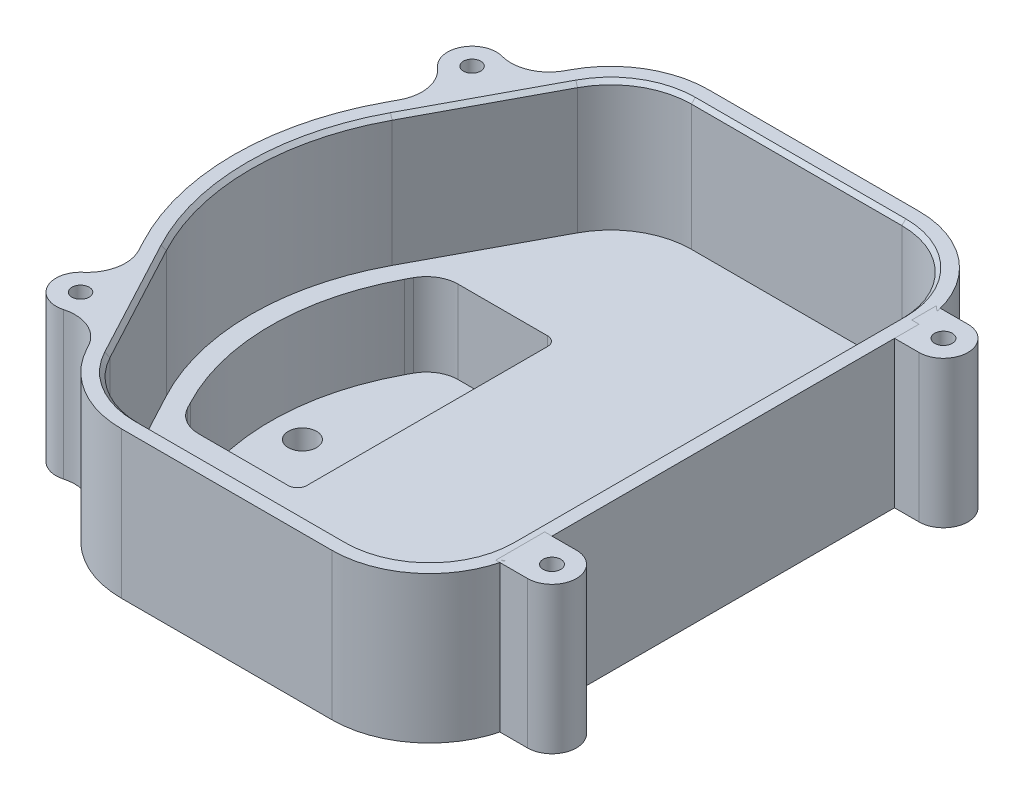
SolidWorks part; units mm, degrees
material "6061-T6 (SS)"
ref_plane "Front Plane" through (0, 0, 0) normal (0, 0, 1) x (1, 0, 0)
ref_plane "Top Plane" through (0, 0, 0) normal (0, 1, 0) x (1, 0, 0)
ref_plane "Right Plane" through (0, 0, 0) normal (1, 0, 0) x (0, 0, -1)
sketch "Sketch1" plane through (0, 0, 0) normal (0, 1, 0) x (1, 0, 0)
  line L0 (-57.15, 0) -> (-57.15, -50000) construction
  line L1 (-25.4, -76.2) -> (-25.4, -101.6) construction
  line L2 (-25.4, -76.2) -> (69.85, -76.2)
  line L3 (-25.4, 76.2) -> (69.85, 76.2)
  line L4 (69.85, -76.2) -> (69.85, 76.2)
  line L5 (-25.4, 76.2) -> (-25.4, 101.6) construction
  line L6 (0, 0) -> (0, -50000) construction
  line L7 (-49.3059, 31.3765) -> (-25.4, 76.2)
  line L8 (-57.15, 0) -> (69.85, 0) construction
  line L9 (-49.3059, -31.3765) -> (-25.4, -76.2)
  arc A0 (-49.3059, -31.3765) -> (-49.3059, 31.3765) centre (9.525, 0) cw
  point P0 (0, 0)
  dimension "D5" = 50.8
  dimension "D1" = 76.2
  dimension "D2" = 25.4
  dimension "D3" = 25.4
  dimension "D4" = 69.85
  dimension "D6" = 127
extrude "Boss-Extrude1" add sketch "Sketch1" along normal blind 38.1
fillet "Fillet1" radius 25.4 4 edges at (-25.4, 19.05, 76.2) (69.85, 19.05, 76.2) (69.85, 19.05, -76.2) (-25.4, 19.05, -76.2)
shell "Shell1" thickness 4.445
sketch "Sketch13" plane through (0, 0, 0) normal (0, -1, 0) x (1, 0, 0)
  line L0 (0, 0) -> (-50000, 0) construction
  line L1 (-2.54, 38.1) -> (-2.54, -38.1)
  line L2 (-2.54, 38.1) -> (-40.2167, 38.1)
  line L3 (-49.3059, 31.3765) -> (-32.5718, 62.7529) construction
  line L4 (-40.2167, -38.1) -> (-2.54, -38.1)
  line L12 (-40.2167, -38.1) -> (-44.5994, -29.8824)
  line L13 (-44.5994, 29.8824) -> (-40.2167, 38.1)
  arc A1 (-49.3059, 31.3765) -> (-49.3059, -31.3765) centre (9.525, 0) ccw construction
  arc A5 (-44.5994, 29.8824) -> (-44.5994, -29.8824) centre (11.43, 0) ccw
  dimension "D3" = 49.53
  dimension "D2" = 63.5
  dimension "D5" = 54.61
  dimension "D1" = 76.2
extrude "nub" add sketch "Sketch13" along normal blind 23.368
fillet "Fillet2" radius 12.7 2 edges at (-40.2167, -11.684, -38.1) (-40.2167, -11.684, 38.1)
fillet "Fillet3" radius 6.858 2 edges at (-2.54, -11.684, -38.1) (-2.54, -11.684, 38.1)
sketch "Sketch8" plane through (0, 4.445, 0) normal (0, 1, 0) x (1, 0, 0)
  line L24 (-6.985, -31.242) -> (-6.985, 31.242)
  line L25 (-32.5967, -33.655) -> (-9.398, -33.655)
  line L26 (-40.6774, -27.7906) -> (-39.8805, -29.2847)
  line L27 (-39.8805, 29.2847) -> (-40.6774, 27.7906)
  line L28 (-32.5967, -33.655) -> (-9.398, -33.655)
  line L29 (-6.985, -31.242) -> (-6.985, 31.242)
  line L30 (-9.398, 33.655) -> (-32.5967, 33.655)
  line L31 (-40.6774, -27.7906) -> (-39.8805, -29.2847)
  line L32 (-39.8805, 29.2847) -> (-40.6774, 27.7906)
  line L33 (-9.398, 33.655) -> (-32.5967, 33.655)
  arc A30 (-6.985, 31.242) -> (-9.398, 33.655) centre (-9.398, 31.242) ccw
  arc A31 (-6.985, 31.242) -> (-9.398, 33.655) centre (-9.398, 31.242) ccw
  arc A32 (-40.6774, 27.7906) -> (-40.6774, -27.7906) centre (11.43, 0) ccw
  arc A33 (-39.8805, -29.2847) -> (-32.5967, -33.655) centre (-32.5967, -25.4) ccw
  arc A34 (-39.8805, -29.2847) -> (-32.5967, -33.655) centre (-32.5967, -25.4) ccw
  arc A35 (-32.5967, 33.655) -> (-39.8805, 29.2847) centre (-32.5967, 25.4) ccw
  arc A36 (-32.5967, 33.655) -> (-39.8805, 29.2847) centre (-32.5967, 25.4) ccw
  arc A37 (-40.6774, 27.7906) -> (-40.6774, -27.7906) centre (11.43, 0) ccw
  arc A38 (-9.398, -33.655) -> (-6.985, -31.242) centre (-9.398, -31.242) ccw
  arc A39 (-9.398, -33.655) -> (-6.985, -31.242) centre (-9.398, -31.242) ccw
  dimension "D1" = 4.445
extrude "Cut-Extrude1" cut sketch "Sketch8" against normal offset from surface (21.463 mm away) 6.35 up to face at (-27.2365, -23.368, 0)
chamfer "Chamfer1" distance 1.016 angle 45 10 edges at (-37.0168, 38.1, 44.9729) (-20.9413, 38.1, 68.7688) (-52.705, 38.1, 0) (17.145, 38.1, 71.755) (-37.0168, 38.1, -44.9729) (59.2674, 38.1, 65.6174) (-20.9413, 38.1, -68.7688) (65.405, 38.1, 0) (17.145, 38.1, -71.755) (59.2674, 38.1, -65.6174)
sketch "Sketch10" plane through (0, 38.1, 0) normal (0, 1, 0) x (1, 0, 0)
  line L0 (69.85, 47.625) -> (69.85, 15.875)
  line L1 (69.85, -50.8) -> (69.85, 50.8) construction
  line L2 (0, 0) -> (50000, 0) construction
  line L3 (69.85, -47.625) -> (69.85, -15.875)
  line L4 (-33.0698, 61.8191) -> (-48.011, 33.8044)
  line L5 (-32.5718, 62.7529) -> (-49.3059, 31.3765) construction
  line L6 (-44.4579, 56.9222) -> (-50.2886, 45.9897) construction
  line L7 (-42.0859, 47.888) -> (40559.6261, -29092.0967) construction
  line L8 (-44.4579, -56.9222) -> (-50.2886, -45.9897) construction
  line L9 (-33.0698, -61.8191) -> (-48.011, -33.8044)
  arc A0 (69.85, 47.625) -> (77.5939, 37.9451) centre (79.7719, 47.625) ccw
  arc A1 (77.5939, 37.9451) -> (77.5939, 25.5549) centre (76.2, 31.75) cw
  arc A2 (77.5939, -25.5549) -> (69.85, -15.875) centre (79.7719, -15.875) cw
  arc A3 (77.5939, 25.5549) -> (69.85, 15.875) centre (79.7719, 15.875) ccw
  arc A4 (77.5939, -37.9451) -> (77.5939, -25.5549) centre (76.2, -31.75) ccw
  arc A5 (69.85, -47.625) -> (77.5939, -37.9451) centre (79.7719, -47.625) cw
  arc A6 (-33.0698, 61.8191) -> (-44.4579, 56.9222) centre (-41.8244, 66.4882) cw
  arc A7 (-44.4579, 56.9222) -> (-50.2886, 45.9897) centre (-46.1433, 50.8) ccw
  arc A8 (-50.2886, 45.9897) -> (-48.011, 33.8044) centre (-56.7656, 38.4735) cw
  arc A9 (-50.2886, -45.9897) -> (-48.011, -33.8044) centre (-56.7656, -38.4735) ccw
  arc A10 (-44.4579, -56.9222) -> (-50.2886, -45.9897) centre (-46.1433, -50.8) cw
  arc A11 (-33.0698, -61.8191) -> (-44.4579, -56.9222) centre (-41.8244, -66.4882) ccw
  point P30 (-40.9388, 47.0647)
  dimension "D1" = 6.35
  dimension "D6" = 6.35
  dimension "D2" = 31.75
  dimension "D3" = 6.35
  dimension "D4" = 31.75
  dimension "D5" = 31.75
  dimension "D7" = 6.35
  dimension "D8" = 50.8
extrude "Boss-Extrude2" add sketch "Sketch10" against normal up to surface (38.1 mm away) up to face at (4.3477, 0, 0)
hole_wizard "#8 Clearance Hole1" positions "Sketch12" profile "Sketch11" hole size "#8" standard "Ansi Inch" end condition through all
sketch "Sketch12" plane through (0, 38.1, 0) normal (0, 1, 0) x (-1, 0, 0)
  arc A0 (44.4579, -56.9222) -> (50.2886, -45.9897) centre (46.1433, -50.8) ccw construction
  arc A1 (50.2886, 45.9897) -> (44.4579, 56.9222) centre (46.1433, 50.8) ccw construction
  arc A2 (-77.5939, 37.9451) -> (-77.5939, 25.5549) centre (-76.2, 31.75) ccw construction
  arc A3 (-77.5939, -25.5549) -> (-77.5939, -37.9451) centre (-76.2, -31.75) ccw construction
  point P0 (46.1433, -50.8)
  point P1 (46.1433, 50.8)
  point P3 (-76.2, 31.75)
  point P5 (-76.2, -31.75)
sketch "Sketch11" plane through (-46.1433, 38.1, -50.8) normal (1, 0, 0) x (0, 0, 1)
  line L0 (0, 0) -> (0, 61.468)
  line L1 (0, 61.468) -> (2.2479, 61.468)
  line L2 (2.2479, 61.468) -> (2.2479, 0)
  line L5 (2.2479, 0) -> (0, 0)
  line L11 (0, -6.35) -> (0, 107.95) construction
  dimension "Thru Hole Dia." = 4.4958
  dimension "Thru Hole Depth" = 61.468
sketch "Sketch14" plane through (0, -23.368, 0) normal (0, -1, 0) x (1, 0, 0)
  line L0 (0, 0) -> (50000, 0) construction
  line L1 (-2.54, -31.242) -> (-2.54, 31.242) construction
  circle A0 centre (-16.51, 22.86) radius 3.675
  circle A1 centre (-16.51, 0) radius 3.675
  circle A2 centre (-16.51, -22.86) radius 3.675
  circle A3 centre (-39.37, 0) radius 3.675
  dimension "D1" = 7.35
  dimension "D2" = 45.72
  dimension "D3" = 22.86
  dimension "D4" = 13.97
extrude "Cut-Extrude2" cut sketch "Sketch14" against normal through all
ref_point "Point1"
ref_plane "Plane1" through (-16.51, 0, 0) normal (-1, 0, 0) x (0, 0, 1)
ref_point "Point2"
ref_point "Point3"
ref_point "Point4"
sketch "Sketch16" plane through (0, -17.018, 0) normal (0, 1, 0) x (1, 0, 0)
  circle A0 centre (-16.51, -22.86) radius 3.6754
  circle A1 centre (-16.51, -22.86) radius 3.8024
  dimension "D1" = 7.3508
  dimension "D2" = 7.6048
sketch "Sketch18" plane through (0, 38.1, 0) normal (0, 1, 0) x (1, 0, 0)
  line L1 (69.85, 47.625) -> (87.7506, 47.625)
  line L2 (69.85, 47.625) -> (69.85, -51.2029)
  line L3 (69.85, -51.2029) -> (87.7506, -51.2029)
  line L4 (87.7506, 47.625) -> (87.7506, -51.2029)
  dimension "D1" = 17.9006
  dimension "D2" = 98.8279
extrude "Cut-Extrude5" cut sketch "Sketch18" against normal through all
sketch "Sketch19" plane through (0, 38.1, 0) normal (0, 1, 0) x (1, 0, 0)
  line L0 (69.85, -50.8) -> (69.85, 50.8) construction
  line L1 (0, 0) -> (115.4293, 0) construction
  line L3 (76.2, 57.15) -> (67.9646, 57.15)
  line L4 (67.9646, 57.15) -> (67.9646, 44.45)
  line L5 (67.9646, 44.45) -> (76.2, 44.45)
  line L6 (67.9646, -44.45) -> (76.2, -44.45)
  line L7 (67.9646, -57.15) -> (67.9646, -44.45)
  line L8 (76.2, -57.15) -> (67.9646, -57.15)
  arc A0 (76.2, 44.45) -> (76.2, 57.15) centre (76.2, 50.8) ccw
  circle A1 centre (76.2, 50.8) radius 2.286
  circle A5 centre (76.2, -50.8) radius 2.286
  arc A6 (76.2, -44.45) -> (76.2, -57.15) centre (76.2, -50.8) cw
  point P4 (69.85, 0)
  dimension "D1" = 12.7
  dimension "D4" = 4.572
  dimension "D2" = 6.35
  dimension "D3" = 50.8
  dimension "D5" = 8.2354
extrude "Boss-Extrude4" add sketch "Sketch19" against normal up to surface (38.1 mm away) separate body up to face at (-17.274, 0, 0)
